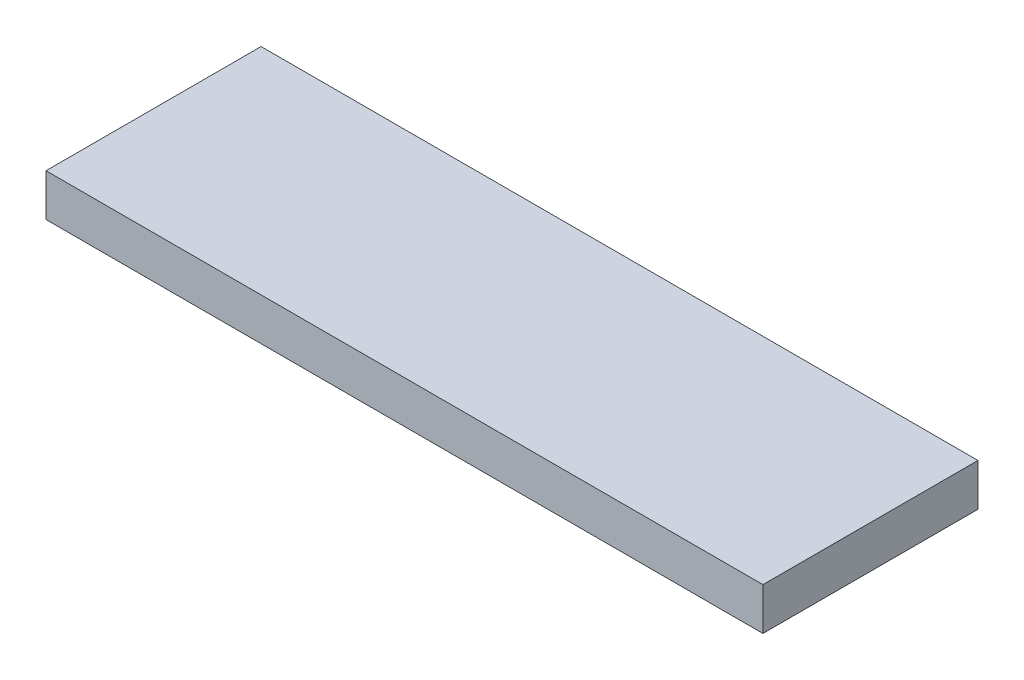
SolidWorks part; units mm, degrees
ref_plane "Front Plane" through (0, 0, 0) normal (0, 0, 1) x (1, 0, 0)
ref_plane "Top Plane" through (0, 0, 0) normal (0, 1, 0) x (1, 0, 0)
ref_plane "Right Plane" through (0, 0, 0) normal (1, 0, 0) x (0, 0, -1)
sketch "Sketch1" plane through (0, 0, 0) normal (0, 1, 0) x (1, 0, 0)
  line L1 (-24.9461, 33.0472) -> (25.0539, 33.0472)
  line L2 (-24.9461, 33.0472) -> (-24.9461, 18.0472)
  line L3 (-24.9461, 18.0472) -> (25.0539, 18.0472)
  line L4 (25.0539, 33.0472) -> (25.0539, 18.0472)
  dimension "D1" = 15
  dimension "D2" = 50
extrude "Boss-Extrude1" add sketch "Sketch1" along normal blind 2.95
